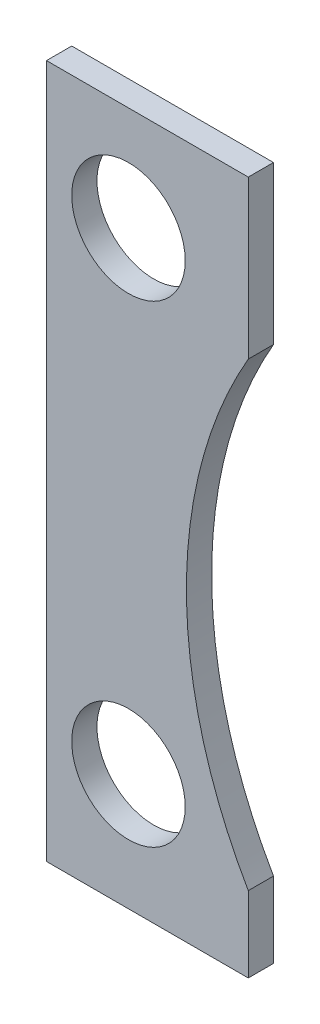
SolidWorks part; units mm, degrees
ref_plane "Front Plane" through (0, 0, 0) normal (0, 0, 1) x (1, 0, 0)
ref_plane "Top Plane" through (0, 0, 0) normal (0, 1, 0) x (1, 0, 0)
ref_plane "Right Plane" through (0, 0, 0) normal (1, 0, 0) x (0, 0, -1)
sketch "Çizim1" plane through (0, 0, 0) normal (0, 0, 1) x (1, 0, 0)
  line L0 (0, 0) -> (0, 110)
  line L1 (0, 110) -> (32, 110)
  line L2 (32, 110) -> (32, 85)
  line L3 (0, 0) -> (32, 0)
  line L4 (32, 0) -> (32, 12)
  arc A0 (32, 12) -> (32, 85) centre (95, 48.5) cw
  dimension "D1" = 110
  dimension "D2" = 32
  dimension "D3" = 25
  dimension "D4" = 12
  dimension "D5" = 95
extrude "Yükseklik-Ekstrüzyon1" add sketch "Çizim1" along normal mid plane 4
sketch "Çizim2" plane through (0, 0, 2) normal (0, 0, 1) x (1, 0, 0)
  line L0 (0, 110) -> (0, 0) construction
  line L1 (32, 110) -> (0, 110) construction
  line L2 (0, 0) -> (32, 0) construction
  circle A0 centre (13, 93.5) radius 9
  circle A1 centre (13, 18.5) radius 9
  dimension "D1" = 18
  dimension "D2" = 13
  dimension "D3" = 16.5
  dimension "D4" = 18.5
  dimension "D5" = 13
extrude "Kes-Ekstrüzyon1" cut sketch "Çizim2" against normal through all
